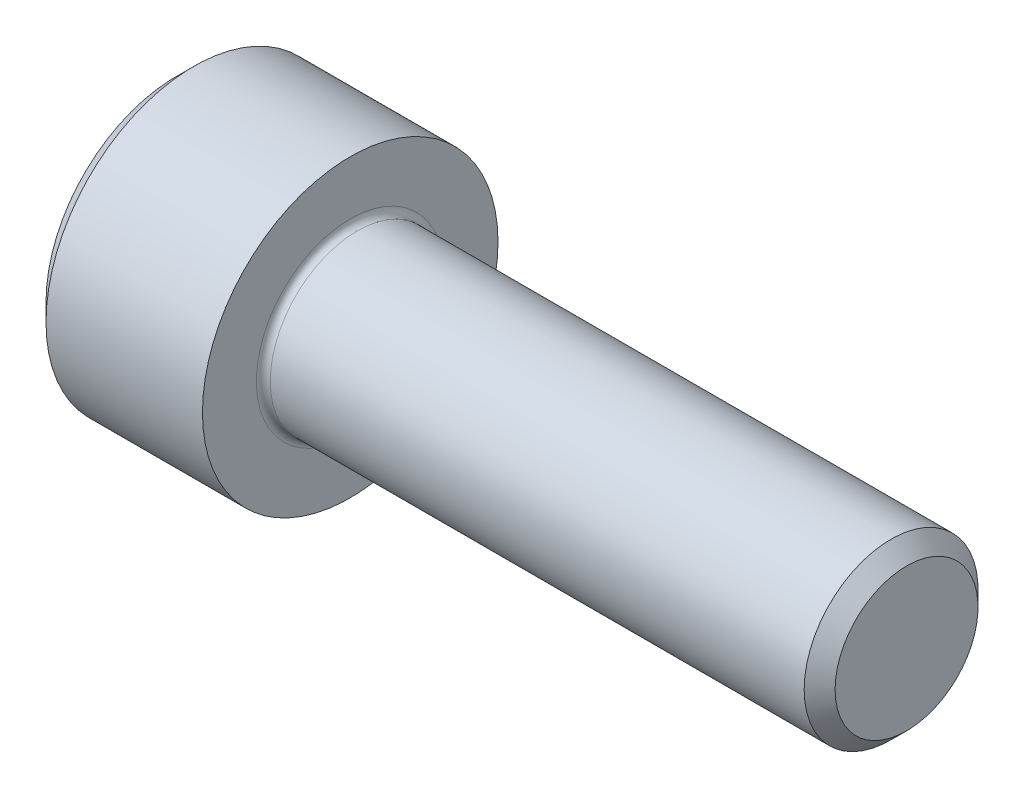
SolidWorks part; units mm, degrees
material "Plain Carbon Steel"
ref_plane "Plane1" through (0, 0, 0) normal (0, 0, 1) x (1, 0, 0)
ref_plane "Plane2" through (0, 0, 0) normal (0, 1, 0) x (1, 0, 0)
ref_plane "Plane3" through (0, 0, 0) normal (1, 0, 0) x (0, 0, -1)
sketch "BodySke" plane through (0, 0, 0) normal (0, 0, 1) x (1, 0, 0)
  line L0 (0, 0) -> (0, 3.75)
  line L1 (0.5, 4.25) -> (5, 4.25)
  line L2 (5, 4.25) -> (5, 2.5)
  line L3 (5, 2.5) -> (20.555, 2.5)
  line L4 (21, 2.055) -> (21, 0)
  line L5 (21, 0) -> (0, 0)
  line L6 (-31.75, 0) -> (127, 0) construction
  line L7 (0, 3.75) -> (0.5, 4.25)
  line L8 (21, 2.055) -> (20.555, 2.5)
  line L9 (0, -3.75) -> (0.5, -4.25) construction
  line L10 (21, -2.055) -> (20.555, -2.5) construction
  line L11 (5.8, 9.525) -> (5.8, 3.175) construction
  line L12 (5, 9.525) -> (5, 3.175) construction
  line L13 (-29, 9.525) -> (-29, 3.175) construction
  dimension "Diameter" = 5
  dimension "Head_ht" = 5
  dimension "Length" = 16
  dimension "Body_ch_ang" = 45
  dimension "Head_dia" = 8.5
  dimension "Head_ch_ang" = 45
  dimension "Minor_dia" = 4.11
  dimension "Advance" = 0.8
  dimension "Thread_nom" = 16
  dimension "Thread_length" = 50
  dimension "Head_ch_ht" = 0.5
revolve "Base-Revolve" add sketch "BodySke"
cosmetic thread "ThreadCosmetic"
fillet "Fillet1" radius 0.2 1 edges at (5, 0, 2.5)
sketch "Sketch2" plane through (0, 0, 0) normal (0, 0, 1) x (1, 0, 0)
  line L0 (0, 2.042) -> (2.5, 2.042)
  line L1 (2.5, 2.042) -> (3.6789, 0)
  line L2 (-31.75, 0) -> (127, 0) construction
  line L3 (3.6789, 0) -> (0, 0)
  line L4 (0, 0) -> (0, 2.042)
  line L5 (0, 3.75) -> (0, -3.75) construction
  line L6 (0, 0) -> (47.625, 0) construction
  line L7 (5, -4.25) -> (5, 4.25) construction
  dimension "D1" = 2.042
  dimension "D2" = 60
  dimension "Wall_thickness" = 2.5
revolve "Hex-PreBroach" cut sketch "Sketch2" angle 360 about L6
sketch "Sketch3" plane through (0, 0, 0) normal (-1, 0, 0) x (0, 0.5, 0.866)
  line L0 (1.1789, 2.042) -> (-1.1789, 2.042)
  line L1 (-1.1789, 2.042) -> (-2.3579, 0)
  line L2 (1.1789, 2.042) -> (2.3579, 0)
  line L3 (1.1789, -2.042) -> (2.3579, 0)
  line L4 (1.1789, -2.042) -> (-1.1789, -2.042)
  line L5 (-1.1789, -2.042) -> (-2.3579, 0)
  dimension "D1" = 2.042
  dimension "D2" = 2.042
  dimension "Hex_size" = 4.084
extrude "Hex" cut sketch "Sketch3" against normal blind 2.5
